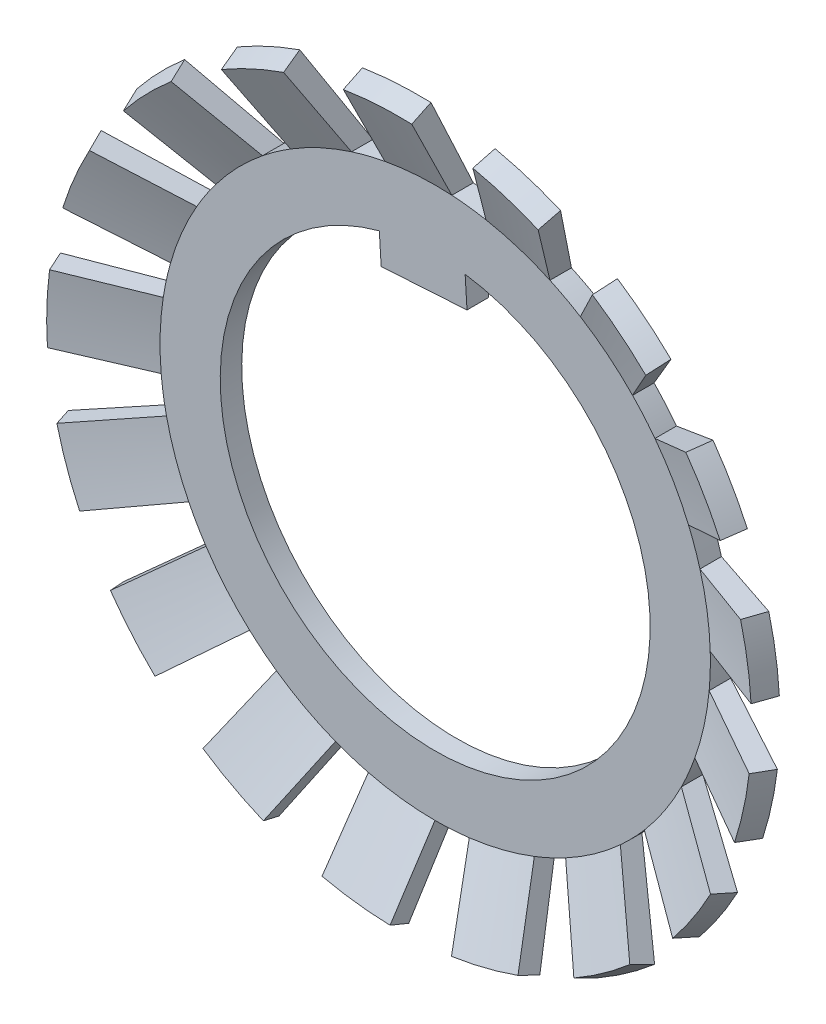
SolidWorks part; units mm, degrees
ref_plane "Front" through (0, 0, 0) normal (0, 0, 1) x (1, 0, 0)
ref_plane "Top" through (0, 0, 0) normal (0, 1, 0) x (1, 0, 0)
ref_plane "Right" through (0, 0, 0) normal (1, 0, 0) x (0, 0, -1)
sketch "Sketch1" plane through (0, 0, 0) normal (1, 0, 0) x (0, 1, 0)
  line L0 (0, -3.3466) -> (-16, -3.3466)
  line L1 (-16, -3.3466) -> (-21, -1.1439)
  line L2 (0, 5.8236) -> (0, -8.1378) construction
  line L4 (-20.4961, 0) -> (-16, -2.0966)
  line L5 (-16, -2.0966) -> (0, -2.0966)
  line L6 (0, -2.0966) -> (0, -3.3466)
  line L7 (-21, -1.1439) -> (-20.4961, 0)
  dimension "D1" = 32
  dimension "S1" = 1.25
  dimension "Angle" = 65
  dimension "D" = 42
  dimension "S" = 1.25
revolve "Base-Extrude" add sketch "Sketch1" angle 360 about L2
sketch "Sketch2" plane through (-2.4044, 1.0036, -3.3466) normal (0, 0, -1) x (-1, 0, 0)
  line L0 (-20.5909, 9.4964) -> (-2.4044, -1.0036) construction
  line L5 (-15.1825, 8.6255) -> (-19.5095, 11.1789)
  line L6 (-17.1325, 5.248) -> (-21.5073, 7.7187)
  line L9 (-2.4044, 13.9688) -> (-2.4044, -17.023) construction
  line L10 (-2.4044, -1.0036) -> (1.5148, -15.6299) construction
  circle A0 centre (-2.4044, -1.0036) radius 12.5
  arc A2 (-17.1325, 5.248) -> (-15.1825, 8.6255) centre (-2.4044, -1.0036) ccw
  circle A3 centre (-2.4044, -1.0036) radius 21 construction
  arc A4 (-19.5095, 11.1789) -> (-21.5073, 7.7187) centre (-2.4044, -1.0036) ccw
  circle A5 centre (-2.4044, -1.0036) radius 16 construction
  dimension "D2" = 2
  dimension "D1" = 25
  dimension "D3" = 1.95
  dimension "D4" = 1.95
  dimension "D9" = 15
extrude "Cut-Extrude" cut sketch "Sketch2" against normal through all flip side to cut
pattern_circular "阵列(圆周)4" count 17 over 360 about axis through (0, 0, 0) along (0, 0, 1) of bodies 109
sketch "草图2" plane through (0, 0, -2.0966) normal (0, 0, 1) x (1, 0, 0)
  line L0 (0, 0) -> (-1.2928, 20.9602) construction
  line L1 (1.8489, 10.634) -> (1.7413, 12.3781)
  line L2 (-3.1416, 10.3262) -> (-3.2492, 12.0703)
  line L3 (-3.1416, 10.3262) -> (1.8489, 10.634)
  line L4 (-14.7653, -13.4344) -> (14.8893, -11.6054) construction
  line L5 (2.4953, 0.1539) -> (1.2025, 21.1141) construction
  line L6 (-2.4953, -0.1539) -> (-3.788, 20.8063) construction
  circle A0 centre (0, 0) radius 12.5 construction
  arc A1 (1.7413, 12.3781) -> (-3.2492, 12.0703) centre (0, 0) ccw
  circle A2 centre (0, 0) radius 21 construction
  circle A3 centre (0, 0) radius 12.5 construction
  dimension "D3" = 23
  dimension "D1" = 2.5
  dimension "D2" = 2.5
extrude "凸台-拉伸1" add sketch "草图2" against normal up to surface (1.25 mm away) up to face at (10.6277, 6.5804, -3.3466)
equation "\"S1@Sketch1\" = \"S@Sketch1\""
equation "\"D1@Extrude1\"=\"S@Sketch1\""
